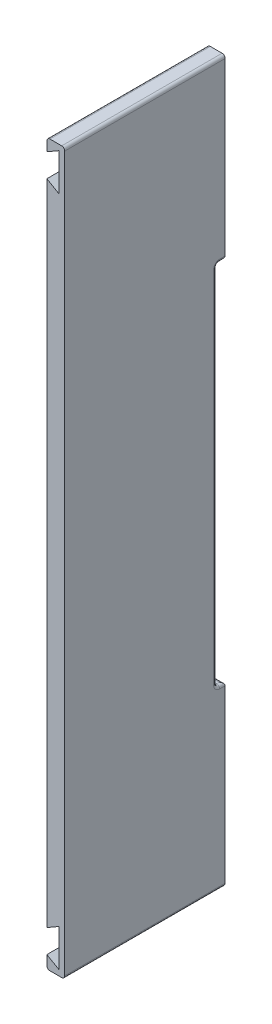
SolidWorks part; units mm, degrees
ref_plane "Front Plane" through (0, 0, 0) normal (0, 0, 1) x (1, 0, 0)
ref_plane "Top Plane" through (0, 0, 0) normal (0, 1, 0) x (1, 0, 0)
ref_plane "Right Plane" through (0, 0, 0) normal (1, 0, 0) x (0, 0, -1)
sketch "Sketch2" plane through (0, 0, 0) normal (0, 0, 1) x (1, 0, 0)
  line L0 (0, 0) -> (0, -4.14)
  line L2 (5.9, -8.6656) -> (5.9, 0)
  line L3 (5.9, 0) -> (0, 0)
  line L4 (0, 0) -> (0, -4.14) construction
  line L5 (0, -19) -> (0, -11.86) construction
  line L6 (0, -4.14) -> (4.0097, -1.825) construction
  line L7 (4.0097, -1.825) -> (4.0097, -14.175)
  line L8 (0, -4.14) -> (4.0097, -1.825)
  line L9 (0, -11.86) -> (4.0097, -14.175)
  line L10 (0, -19) -> (0, -219)
  line L11 (0, -119) -> (59.9435, -119) construction
  line L12 (5.9, -238) -> (0, -238)
  line L13 (5.9, -229.3344) -> (5.9, -238)
  line L15 (0, -238) -> (0, -233.86)
  line L16 (0, -226.14) -> (4.0097, -223.825)
  line L17 (4.0097, -236.175) -> (4.0097, -223.825)
  line L18 (0, -233.86) -> (4.0097, -236.175)
  line L19 (0, -226.14) -> (0, -219)
  line L20 (0, -11.86) -> (0, -19)
  line L21 (5.9, -229.3344) -> (5.9, -8.6656)
  dimension "D1" = 19
  dimension "D2" = 11.9
  dimension "D3" = 4.14
  dimension "D4" = 7.14
  dimension "D5" = 60
  dimension "D6" = 60
  dimension "D7" = 12.35
  dimension "D8" = 200
  dimension "D9" = 5.9
extrude "Boss-Extrude1" add sketch "Sketch2" along normal blind 53
sketch "Sketch3" plane through (0, 0, 0) normal (1, 0, 0) x (0, 0, -1)
  line L0 (0, -119) -> (0, -58.5)
  line L3 (0, -11.86) -> (0, -226.14) construction
  line L4 (0, -119) -> (0, -179.5)
  line L5 (0, -58.5) -> (-2.8, -58.5)
  line L6 (-2.8, -58.5) -> (-2.8, -179.5)
  line L7 (-2.8, -179.5) -> (0, -179.5)
  point P5 (-5.9, -144.9585)
  point P6 (0, -158.9397)
  dimension "D1" = 121
  dimension "D2" = 2.8
  dimension "D3" = 60.5
extrude "Cut-Extrude1" cut sketch "Sketch3" along normal blind 52
sketch "Sketch4" plane through (5.9, 0, 0) normal (1, 0, 0) x (0, 0, -1)
  line L2 (-50, -238) -> (-50, 0)
  line L3 (-50, -235) -> (-50, -5)
  line L8 (-53, -235) -> (0, -235)
  line L9 (-50, -235) -> (-5, -235)
  line L11 (-5, -238) -> (-5, -179.5)
  line L12 (-5, -235) -> (-5, -179.5)
  line L21 (-5.8, -179.5) -> (-5, -179.5)
  line L22 (-5, -5) -> (-5, -58.5)
  line L23 (-53, -5) -> (-5, -5)
  line L24 (-5, -5) -> (-5, -58.5)
  line L25 (-50, -5) -> (-5, -5)
  line L26 (-5.8, -58.5) -> (-5.8, -179.5)
  line L27 (-5.8, -58.5) -> (-5.8, -179.5)
  line L28 (-5.8, -58.5) -> (-5, -58.5)
  dimension "D1" = 3
  dimension "D2" = 3
  dimension "D3" = 5
  dimension "D4" = 5
  dimension "D5" = 3
extrude "Cut-Extrude2" [suppressed] cut sketch "Sketch4" against normal blind 1
fillet "Fillet1" radius 1 10 edges at (5.9, -58.5, 1.4) (0, -58.5, 1.4) (0, -179.5, 1.4) (5.9, -179.5, 1.4) (2.95, -58.5, 0) (2.95, -58.5, 2.8) (0, -119, 2.8) (5.9, -119, 2.8) (2.95, -179.5, 2.8) (2.95, -179.5, 0)
fillet "Fillet2" radius 1 4 edges at (0, -238, 26.5) (5.9, -238, 26.5) (5.9, 0, 26.5) (0, 0, 26.5)
